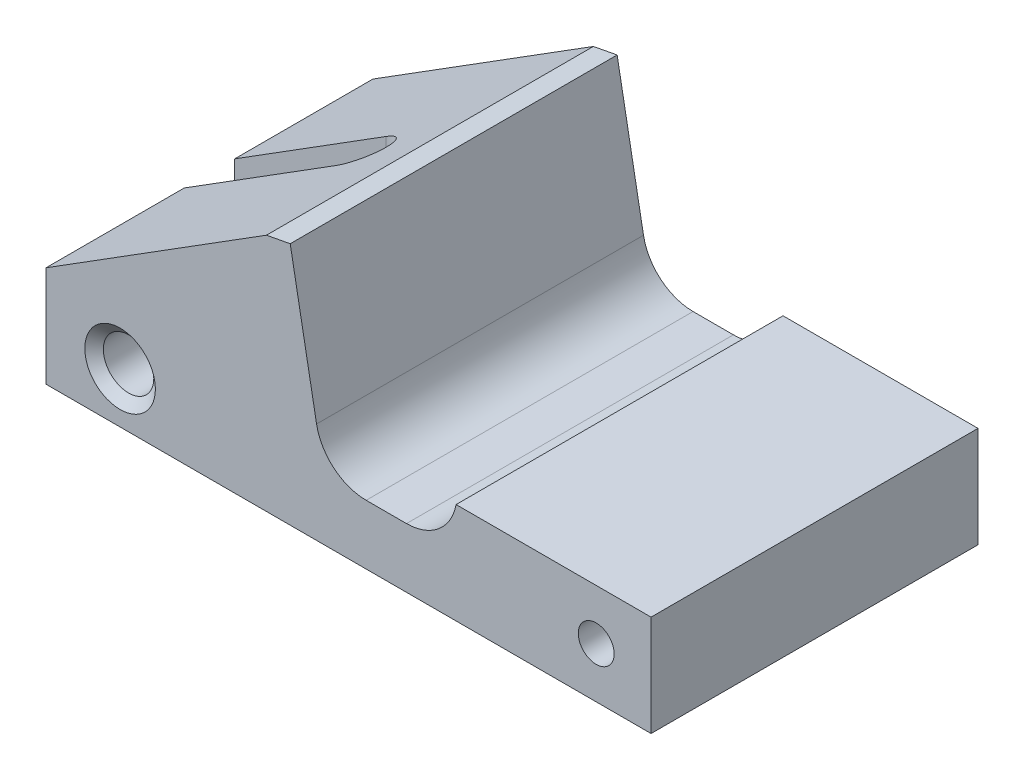
SolidWorks part; units mm, degrees
material "6061-T6 (SS)"
ref_plane "Front Plane" through (0, 0, 0) normal (0, 0, 1) x (1, 0, 0)
ref_plane "Top Plane" through (0, 0, 0) normal (0, 1, 0) x (1, 0, 0)
ref_plane "Right Plane" through (0, 0, 0) normal (1, 0, 0) x (0, 0, -1)
sketch "Sketch1" plane through (0, 0, 0) normal (0, 0, 1) x (1, 0, 0)
  line L0 (-76.567, -68.5403) -> (-62.6865, -59.8235)
  line L1 (-76.567, -68.5403) -> (-38.467, -68.5403)
  line L2 (-76.567, -68.5403) -> (-76.567, -74.8903)
  line L3 (-76.567, -74.8903) -> (-38.467, -74.8903)
  line L4 (-38.467, -68.5403) -> (-38.467, -74.8903)
  line L5 (-62.6865, -59.8235) -> (-61.1892, -59.5393)
  line L6 (-61.1892, -59.5393) -> (-59.5301, -68.5403)
  dimension "D1" = 6.35
  dimension "D2" = 38.1
extrude "Boss-Extrude1" add sketch "Sketch1" along normal offset from surface (20.5861 mm away) 1.27 from offset 1.27
sketch "Sketch2" plane through (26.5539, -74.8903, 0) normal (0, 1, 0) x (1, 0, 0)
  line L0 (-103.1209, -11.5631) -> (-93.5959, -11.5631) construction
  line L1 (-103.1209, -21.8561) -> (-103.1209, -1.27) construction
  line L2 (-103.1209, -13.1506) -> (-93.5959, -13.1506)
  line L3 (-103.1209, -9.9756) -> (-93.5959, -9.9756)
  arc A0 (-103.1209, -13.1506) -> (-103.1209, -9.9756) centre (-103.1209, -11.5631) cw
  arc A1 (-93.5959, -13.1506) -> (-93.5959, -9.9756) centre (-93.5959, -11.5631) ccw
  dimension "D1" = 1.5875
  dimension "D3" = 9.525
  dimension "D2" = 1.5875
extrude "Cut-Extrude1" cut sketch "Sketch2" along normal through all
hole_wizard "1/8 (0.125) Diameter Hole1" positions "Sketch4" profile "Sketch3" hole size "1/8" standard "ANSI Inch" end condition through all
sketch "Sketch4" plane through (0, 0, 21.8561) normal (0, 0, 1) x (1, 0, 0)
  line L0 (-71.9014, -71.7153) -> (-71.9014, -92.3503) construction
  line L2 (-75.8114, -97.0903) -> (-75.8114, -139.1903) construction
  line L3 (-76.567, -71.7153) -> (-38.467, -71.7153) construction
  line L4 (-76.567, -74.8903) -> (-76.567, -68.5403) construction
  line L5 (-38.467, -74.8903) -> (-38.467, -68.5403) construction
  point P0 (-71.9014, -71.7153)
sketch "Sketch3" plane through (-71.9014, -71.7153, 21.8561) normal (1, 0, 0) x (0, -1, 0)
  line L0 (0, 0) -> (0, 20.5861)
  line L1 (0, 20.5861) -> (1.5875, 20.5861)
  line L2 (1.5875, 20.5861) -> (1.5875, 0.5328)
  line L3 (1.5875, 0.5328) -> (2.2225, 0)
  line L5 (2.2225, 0) -> (0, 0)
  line L6 (-1.5875, 0.5328) -> (-2.2225, 0) construction
  line L11 (0, -6.35) -> (0, 107.95) construction
  dimension "Thru Hole Dia." = 3.175
  dimension "Thru Hole Depth" = 20.5861
  dimension "Near C'Sink Dia." = 4.445
  dimension "Near C'Sink Angle" = 100
hole_wizard "#4-40 Tapped Hole1" positions "Sketch6" profile "Sketch5" tap size "#4-40" standard "ANSI Inch" end condition through all
sketch "Sketch6" plane through (0, 0, 21.8561) normal (0, 0, 1) x (1, 0, 0)
  line L0 (-38.467, -74.8903) -> (-38.467, -68.5403) construction
  point P0 (-41.9214, -71.7153)
  point P7 (-38.467, -71.7153)
  dimension "D1" = 3.4544
sketch "Sketch5" plane through (-41.9214, -71.7153, 21.8561) normal (1, 0, 0) x (0, -1, 0)
  line L0 (0, 0) -> (0, 20.5861)
  line L1 (0, 20.5861) -> (1.1303, 20.5861)
  line L2 (1.1303, 20.5861) -> (1.1303, 0)
  line L5 (1.1303, 0) -> (0, 0)
  line L11 (0, -6.35) -> (0, 107.95) construction
  dimension "Thru Tap Drill Dia." = 2.2606
  dimension "Thru Tap Drill Depth" = 20.5861
cosmetic thread "Hole Thread1" parameters "D2"=2.8448
sketch "Sketch7" plane through (0, 0, 21.8561) normal (0, 0, 1) x (1, 0, 0)
  line L3 (-53.8677, -67.9648) -> (-56.4077, -67.9648) construction
  line L5 (-53.8677, -71.1398) -> (-56.4077, -71.1398)
  line L6 (-53.8677, -64.7898) -> (-56.4077, -64.7898)
  line L7 (-59.5301, -68.5403) -> (-61.1892, -59.5393) construction
  arc A0 (-53.8677, -71.1398) -> (-53.8677, -64.7898) centre (-53.8677, -67.9648) ccw
  arc A1 (-56.4077, -64.7898) -> (-56.4077, -71.1398) centre (-56.4077, -67.9648) ccw
  point P2 (-59.5301, -68.5403)
  point P3 (-59.5827, -67.9648)
  point P4 (-55.1377, -67.9648)
  point P17 (-50.6927, -67.9648)
  dimension "D1" = 3.175
  dimension "D2" = 8.89
extrude "Cut-Extrude2" cut sketch "Sketch7" against normal through all
